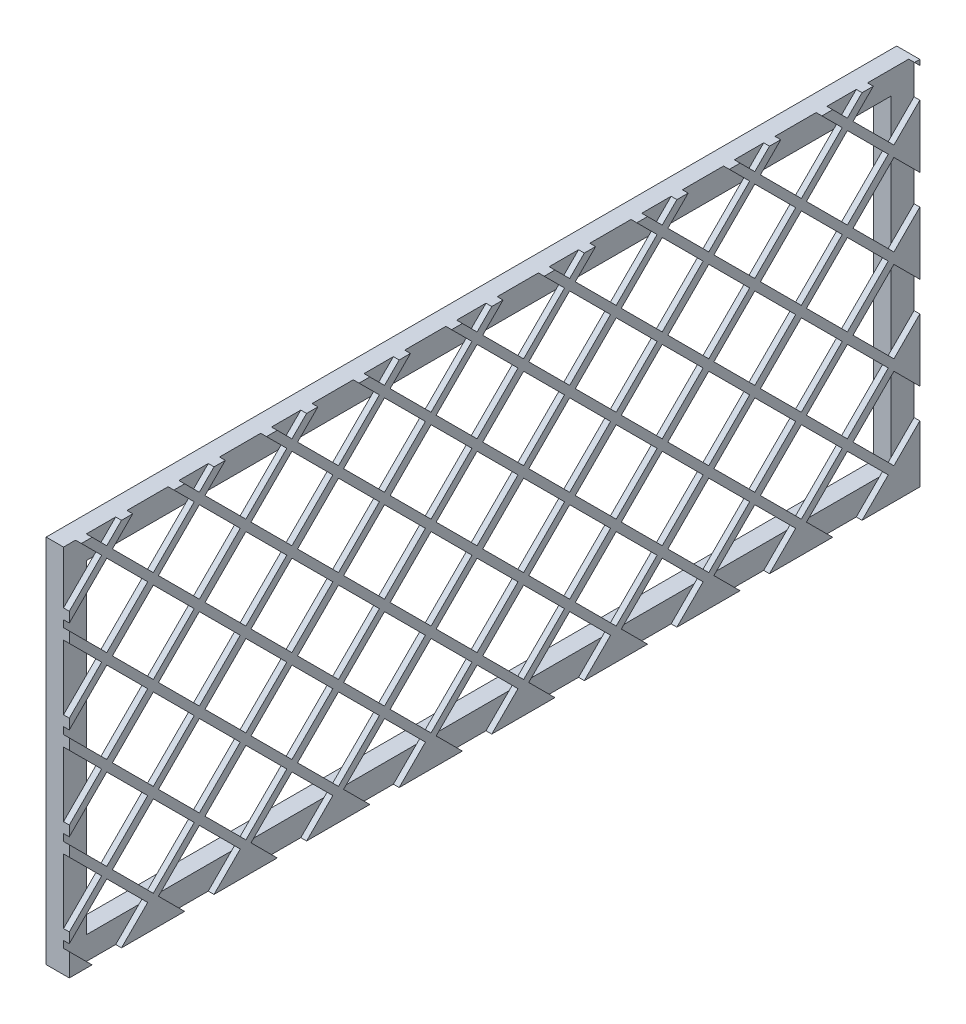
SolidWorks part; units mm, degrees
ref_plane "Front" through (0, 0, 0) normal (0, 0, 1) x (1, 0, 0)
ref_plane "Top" through (0, 0, 0) normal (0, 1, 0) x (1, 0, 0)
ref_plane "Right" through (0, 0, 0) normal (1, 0, 0) x (0, 0, -1)
sketch "Sketch1" plane through (0, 0, 0) normal (1, 0, 0) x (0, 0, -1)
  line L1 (-98.425, -3.313) -> (368.3, -3.313)
  line L2 (-98.425, -3.313) -> (-98.425, -206.513)
  line L3 (-98.425, -206.513) -> (368.3, -206.513)
  line L4 (368.3, -3.313) -> (368.3, -206.513)
  line L5 (-85.725, -16.013) -> (355.6, -16.013)
  line L6 (-85.725, -16.013) -> (-85.725, -193.813)
  line L7 (-85.725, -193.813) -> (355.6, -193.813)
  line L8 (355.6, -16.013) -> (355.6, -193.813)
  dimension "D1" = 12.7
  dimension "D2" = 12.7
  dimension "D3" = 12.7
  dimension "D4" = 12.7
  dimension "D5" = 203.2
  dimension "D6" = 466.725
extrude "Boss-Extrude1" add sketch "Sketch1" along normal blind 12.7
sketch "Sketch2" plane through (12.7, 0, 0) normal (1, 0, 0) x (0, 0, -1)
  line L1 (-85.725, -16.013) -> (355.6, -16.013)
  line L2 (-85.725, -16.013) -> (-85.725, -193.813)
  line L3 (-85.725, -193.813) -> (355.6, -193.813)
  line L4 (355.6, -16.013) -> (355.6, -193.813)
extrude "Boss-Extrude2" add sketch "Sketch2" against normal blind 3.175
sketch "Sketch3" plane through (9.525, 0, 0) normal (-1, 0, 0) x (0, 0, 1)
  line L0 (-350.9847, 163.4755) -> (-328.5341, 185.9261)
  line L1 (-328.5341, 185.9261) -> (-306.0835, 163.4755)
  line L2 (-350.9847, 163.4755) -> (-328.5341, 141.0249)
  line L3 (-328.5341, 141.0249) -> (-306.0835, 163.4755)
  line L8 (-354.0779, 211.1824) -> (-331.6272, 188.7318)
  line L9 (-331.6272, 188.7318) -> (-354.0779, 166.2811)
  line L10 (-354.0779, 166.2811) -> (-376.5285, 188.7318)
  line L11 (-376.5285, 188.7318) -> (-354.0779, 211.1824)
  line L12 (-300.1847, 163.4755) -> (-277.7341, 185.9261)
  line L13 (-277.7341, 185.9261) -> (-255.2835, 163.4755)
  line L14 (-300.1847, 163.4755) -> (-277.7341, 141.0249)
  line L15 (-277.7341, 141.0249) -> (-255.2835, 163.4755)
  line L16 (-280.8272, 188.7318) -> (-303.2779, 166.2811)
  line L17 (-303.2779, 166.2811) -> (-325.7285, 188.7318)
  line L18 (-325.7285, 188.7318) -> (-303.2779, 211.1824)
  line L19 (-303.2779, 211.1824) -> (-280.8272, 188.7318)
  line L20 (-249.3847, 163.4755) -> (-226.9341, 185.9261)
  line L21 (-226.9341, 185.9261) -> (-204.4835, 163.4755)
  line L22 (-249.3847, 163.4755) -> (-226.9341, 141.0249)
  line L23 (-226.9341, 141.0249) -> (-204.4835, 163.4755)
  line L24 (-230.0272, 188.7318) -> (-252.4779, 166.2811)
  line L25 (-252.4779, 166.2811) -> (-274.9285, 188.7318)
  line L26 (-274.9285, 188.7318) -> (-252.4779, 211.1824)
  line L27 (-252.4779, 211.1824) -> (-230.0272, 188.7318)
  line L28 (-198.5847, 163.4755) -> (-176.1341, 185.9261)
  line L29 (-176.1341, 185.9261) -> (-153.6835, 163.4755)
  line L30 (-198.5847, 163.4755) -> (-176.1341, 141.0249)
  line L31 (-176.1341, 141.0249) -> (-153.6835, 163.4755)
  line L32 (-179.2272, 188.7318) -> (-201.6779, 166.2811)
  line L33 (-201.6779, 166.2811) -> (-224.1285, 188.7318)
  line L34 (-224.1285, 188.7318) -> (-201.6779, 211.1824)
  line L35 (-201.6779, 211.1824) -> (-179.2272, 188.7318)
  line L36 (-147.7847, 163.4755) -> (-125.3341, 185.9261)
  line L37 (-125.3341, 185.9261) -> (-102.8835, 163.4755)
  line L38 (-147.7847, 163.4755) -> (-125.3341, 141.0249)
  line L39 (-125.3341, 141.0249) -> (-102.8835, 163.4755)
  line L40 (-128.4272, 188.7318) -> (-150.8779, 166.2811)
  line L41 (-150.8779, 166.2811) -> (-173.3285, 188.7318)
  line L42 (-173.3285, 188.7318) -> (-150.8779, 211.1824)
  line L43 (-150.8779, 211.1824) -> (-128.4272, 188.7318)
  line L44 (-96.9847, 163.4755) -> (-74.5341, 185.9261)
  line L45 (-74.5341, 185.9261) -> (-52.0835, 163.4755)
  line L46 (-96.9847, 163.4755) -> (-74.5341, 141.0249)
  line L47 (-74.5341, 141.0249) -> (-52.0835, 163.4755)
  line L48 (-77.6272, 188.7318) -> (-100.0779, 166.2811)
  line L49 (-100.0779, 166.2811) -> (-122.5285, 188.7318)
  line L50 (-122.5285, 188.7318) -> (-100.0779, 211.1824)
  line L51 (-100.0779, 211.1824) -> (-77.6272, 188.7318)
  line L52 (-46.1847, 163.4755) -> (-23.7341, 185.9261)
  line L53 (-23.7341, 185.9261) -> (-1.2835, 163.4755)
  line L54 (-46.1847, 163.4755) -> (-23.7341, 141.0249)
  line L55 (-23.7341, 141.0249) -> (-1.2835, 163.4755)
  line L56 (-26.8272, 188.7318) -> (-49.2779, 166.2811)
  line L57 (-49.2779, 166.2811) -> (-71.7285, 188.7318)
  line L58 (-71.7285, 188.7318) -> (-49.2779, 211.1824)
  line L59 (-49.2779, 211.1824) -> (-26.8272, 188.7318)
  line L60 (4.6153, 163.4755) -> (27.0659, 185.9261)
  line L61 (27.0659, 185.9261) -> (49.5165, 163.4755)
  line L62 (4.6153, 163.4755) -> (27.0659, 141.0249)
  line L63 (27.0659, 141.0249) -> (49.5165, 163.4755)
  line L64 (23.9728, 188.7318) -> (1.5221, 166.2811)
  line L65 (1.5221, 166.2811) -> (-20.9285, 188.7318)
  line L66 (-20.9285, 188.7318) -> (1.5221, 211.1824)
  line L67 (1.5221, 211.1824) -> (23.9728, 188.7318)
  line L68 (55.4153, 163.4755) -> (77.8659, 185.9261)
  line L69 (77.8659, 185.9261) -> (100.3165, 163.4755)
  line L70 (55.4153, 163.4755) -> (77.8659, 141.0249)
  line L71 (77.8659, 141.0249) -> (100.3165, 163.4755)
  line L72 (74.7728, 188.7318) -> (52.3221, 166.2811)
  line L73 (52.3221, 166.2811) -> (29.8715, 188.7318)
  line L74 (29.8715, 188.7318) -> (52.3221, 211.1824)
  line L75 (52.3221, 211.1824) -> (74.7728, 188.7318)
  line L76 (106.2153, 163.4755) -> (128.6659, 185.9261)
  line L77 (128.6659, 185.9261) -> (151.1165, 163.4755)
  line L78 (106.2153, 163.4755) -> (128.6659, 141.0249)
  line L79 (128.6659, 141.0249) -> (151.1165, 163.4755)
  line L80 (125.5728, 188.7318) -> (103.1221, 166.2811)
  line L81 (103.1221, 166.2811) -> (80.6715, 188.7318)
  line L82 (80.6715, 188.7318) -> (103.1221, 211.1824)
  line L83 (103.1221, 211.1824) -> (125.5728, 188.7318)
  line L84 (157.0153, 163.4755) -> (179.4659, 185.9261)
  line L85 (179.4659, 185.9261) -> (201.9165, 163.4755)
  line L86 (157.0153, 163.4755) -> (179.4659, 141.0249)
  line L87 (179.4659, 141.0249) -> (201.9165, 163.4755)
  line L88 (176.3728, 188.7318) -> (153.9221, 166.2811)
  line L89 (153.9221, 166.2811) -> (131.4715, 188.7318)
  line L90 (131.4715, 188.7318) -> (153.9221, 211.1824)
  line L91 (153.9221, 211.1824) -> (176.3728, 188.7318)
  line L92 (207.8153, 163.4755) -> (230.2659, 185.9261)
  line L93 (230.2659, 185.9261) -> (252.7165, 163.4755)
  line L94 (207.8153, 163.4755) -> (230.2659, 141.0249)
  line L95 (230.2659, 141.0249) -> (252.7165, 163.4755)
  line L96 (227.1728, 188.7318) -> (204.7221, 166.2811)
  line L97 (204.7221, 166.2811) -> (182.2715, 188.7318)
  line L98 (182.2715, 188.7318) -> (204.7221, 211.1824)
  line L99 (204.7221, 211.1824) -> (227.1728, 188.7318)
  line L100 (258.6153, 163.4755) -> (281.0659, 185.9261)
  line L101 (281.0659, 185.9261) -> (303.5165, 163.4755)
  line L102 (258.6153, 163.4755) -> (281.0659, 141.0249)
  line L103 (281.0659, 141.0249) -> (303.5165, 163.4755)
  line L104 (277.9728, 188.7318) -> (255.5221, 166.2811)
  line L105 (255.5221, 166.2811) -> (233.0715, 188.7318)
  line L106 (233.0715, 188.7318) -> (255.5221, 211.1824)
  line L107 (255.5221, 211.1824) -> (277.9728, 188.7318)
  line L108 (-300.1847, 112.6755) -> (-277.7341, 135.1261)
  line L109 (-277.7341, 135.1261) -> (-255.2835, 112.6755)
  line L110 (-300.1847, 112.6755) -> (-277.7341, 90.2249)
  line L111 (-277.7341, 90.2249) -> (-255.2835, 112.6755)
  line L112 (-280.8272, 137.9318) -> (-303.2779, 115.4811)
  line L113 (-303.2779, 115.4811) -> (-325.7285, 137.9318)
  line L114 (-325.7285, 137.9318) -> (-303.2779, 160.3824)
  line L115 (-303.2779, 160.3824) -> (-280.8272, 137.9318)
  line L116 (-249.3847, 112.6755) -> (-226.9341, 135.1261)
  line L117 (-226.9341, 135.1261) -> (-204.4835, 112.6755)
  line L118 (-249.3847, 112.6755) -> (-226.9341, 90.2249)
  line L119 (-226.9341, 90.2249) -> (-204.4835, 112.6755)
  line L120 (-230.0272, 137.9318) -> (-252.4779, 115.4811)
  line L121 (-252.4779, 115.4811) -> (-274.9285, 137.9318)
  line L122 (-274.9285, 137.9318) -> (-252.4779, 160.3824)
  line L123 (-252.4779, 160.3824) -> (-230.0272, 137.9318)
  line L124 (-198.5847, 112.6755) -> (-176.1341, 135.1261)
  line L125 (-176.1341, 135.1261) -> (-153.6835, 112.6755)
  line L126 (-198.5847, 112.6755) -> (-176.1341, 90.2249)
  line L127 (-176.1341, 90.2249) -> (-153.6835, 112.6755)
  line L128 (-179.2272, 137.9318) -> (-201.6779, 115.4811)
  line L129 (-201.6779, 115.4811) -> (-224.1285, 137.9318)
  line L130 (-224.1285, 137.9318) -> (-201.6779, 160.3824)
  line L131 (-201.6779, 160.3824) -> (-179.2272, 137.9318)
  line L132 (-147.7847, 112.6755) -> (-125.3341, 135.1261)
  line L133 (-125.3341, 135.1261) -> (-102.8835, 112.6755)
  line L134 (-147.7847, 112.6755) -> (-125.3341, 90.2249)
  line L135 (-125.3341, 90.2249) -> (-102.8835, 112.6755)
  line L136 (-128.4272, 137.9318) -> (-150.8779, 115.4811)
  line L137 (-150.8779, 115.4811) -> (-173.3285, 137.9318)
  line L138 (-173.3285, 137.9318) -> (-150.8779, 160.3824)
  line L139 (-150.8779, 160.3824) -> (-128.4272, 137.9318)
  line L140 (-96.9847, 112.6755) -> (-74.5341, 135.1261)
  line L141 (-74.5341, 135.1261) -> (-52.0835, 112.6755)
  line L142 (-96.9847, 112.6755) -> (-74.5341, 90.2249)
  line L143 (-74.5341, 90.2249) -> (-52.0835, 112.6755)
  line L144 (-77.6272, 137.9318) -> (-100.0779, 115.4811)
  line L145 (-100.0779, 115.4811) -> (-122.5285, 137.9318)
  line L146 (-122.5285, 137.9318) -> (-100.0779, 160.3824)
  line L147 (-100.0779, 160.3824) -> (-77.6272, 137.9318)
  line L148 (-46.1847, 112.6755) -> (-23.7341, 135.1261)
  line L149 (-23.7341, 135.1261) -> (-1.2835, 112.6755)
  line L150 (-46.1847, 112.6755) -> (-23.7341, 90.2249)
  line L151 (-23.7341, 90.2249) -> (-1.2835, 112.6755)
  line L152 (-26.8272, 137.9318) -> (-49.2779, 115.4811)
  line L153 (-49.2779, 115.4811) -> (-71.7285, 137.9318)
  line L154 (-71.7285, 137.9318) -> (-49.2779, 160.3824)
  line L155 (-49.2779, 160.3824) -> (-26.8272, 137.9318)
  line L156 (4.6153, 112.6755) -> (27.0659, 135.1261)
  line L157 (27.0659, 135.1261) -> (49.5165, 112.6755)
  line L158 (4.6153, 112.6755) -> (27.0659, 90.2249)
  line L159 (27.0659, 90.2249) -> (49.5165, 112.6755)
  line L160 (23.9728, 137.9318) -> (1.5221, 115.4811)
  line L161 (1.5221, 115.4811) -> (-20.9285, 137.9318)
  line L162 (-20.9285, 137.9318) -> (1.5221, 160.3824)
  line L163 (1.5221, 160.3824) -> (23.9728, 137.9318)
  line L164 (55.4153, 112.6755) -> (77.8659, 135.1261)
  line L165 (77.8659, 135.1261) -> (100.3165, 112.6755)
  line L166 (55.4153, 112.6755) -> (77.8659, 90.2249)
  line L167 (77.8659, 90.2249) -> (100.3165, 112.6755)
  line L168 (74.7728, 137.9318) -> (52.3221, 115.4811)
  line L169 (52.3221, 115.4811) -> (29.8715, 137.9318)
  line L170 (29.8715, 137.9318) -> (52.3221, 160.3824)
  line L171 (52.3221, 160.3824) -> (74.7728, 137.9318)
  line L172 (106.2153, 112.6755) -> (128.6659, 135.1261)
  line L173 (128.6659, 135.1261) -> (151.1165, 112.6755)
  line L174 (106.2153, 112.6755) -> (128.6659, 90.2249)
  line L175 (128.6659, 90.2249) -> (151.1165, 112.6755)
  line L176 (125.5728, 137.9318) -> (103.1221, 115.4811)
  line L177 (103.1221, 115.4811) -> (80.6715, 137.9318)
  line L178 (80.6715, 137.9318) -> (103.1221, 160.3824)
  line L179 (103.1221, 160.3824) -> (125.5728, 137.9318)
  line L180 (157.0153, 112.6755) -> (179.4659, 135.1261)
  line L181 (179.4659, 135.1261) -> (201.9165, 112.6755)
  line L182 (157.0153, 112.6755) -> (179.4659, 90.2249)
  line L183 (179.4659, 90.2249) -> (201.9165, 112.6755)
  line L184 (176.3728, 137.9318) -> (153.9221, 115.4811)
  line L185 (153.9221, 115.4811) -> (131.4715, 137.9318)
  line L186 (131.4715, 137.9318) -> (153.9221, 160.3824)
  line L187 (153.9221, 160.3824) -> (176.3728, 137.9318)
  line L188 (207.8153, 112.6755) -> (230.2659, 135.1261)
  line L189 (230.2659, 135.1261) -> (252.7165, 112.6755)
  line L190 (207.8153, 112.6755) -> (230.2659, 90.2249)
  line L191 (230.2659, 90.2249) -> (252.7165, 112.6755)
  line L192 (227.1728, 137.9318) -> (204.7221, 115.4811)
  line L193 (204.7221, 115.4811) -> (182.2715, 137.9318)
  line L194 (182.2715, 137.9318) -> (204.7221, 160.3824)
  line L195 (204.7221, 160.3824) -> (227.1728, 137.9318)
  line L196 (258.6153, 112.6755) -> (281.0659, 135.1261)
  line L197 (281.0659, 135.1261) -> (303.5165, 112.6755)
  line L198 (258.6153, 112.6755) -> (281.0659, 90.2249)
  line L199 (281.0659, 90.2249) -> (303.5165, 112.6755)
  line L200 (277.9728, 137.9318) -> (255.5221, 115.4811)
  line L201 (255.5221, 115.4811) -> (233.0715, 137.9318)
  line L202 (233.0715, 137.9318) -> (255.5221, 160.3824)
  line L203 (255.5221, 160.3824) -> (277.9728, 137.9318)
  line L204 (-300.1847, 61.8755) -> (-277.7341, 84.3261)
  line L205 (-277.7341, 84.3261) -> (-255.2835, 61.8755)
  line L206 (-300.1847, 61.8755) -> (-277.7341, 39.4249)
  line L207 (-277.7341, 39.4249) -> (-255.2835, 61.8755)
  line L208 (-280.8272, 87.1318) -> (-303.2779, 64.6811)
  line L209 (-303.2779, 64.6811) -> (-325.7285, 87.1318)
  line L210 (-325.7285, 87.1318) -> (-303.2779, 109.5824)
  line L211 (-303.2779, 109.5824) -> (-280.8272, 87.1318)
  line L212 (-249.3847, 61.8755) -> (-226.9341, 84.3261)
  line L213 (-226.9341, 84.3261) -> (-204.4835, 61.8755)
  line L214 (-249.3847, 61.8755) -> (-226.9341, 39.4249)
  line L215 (-226.9341, 39.4249) -> (-204.4835, 61.8755)
  line L216 (-230.0272, 87.1318) -> (-252.4779, 64.6811)
  line L217 (-252.4779, 64.6811) -> (-274.9285, 87.1318)
  line L218 (-274.9285, 87.1318) -> (-252.4779, 109.5824)
  line L219 (-252.4779, 109.5824) -> (-230.0272, 87.1318)
  line L220 (-198.5847, 61.8755) -> (-176.1341, 84.3261)
  line L221 (-176.1341, 84.3261) -> (-153.6835, 61.8755)
  line L222 (-198.5847, 61.8755) -> (-176.1341, 39.4249)
  line L223 (-176.1341, 39.4249) -> (-153.6835, 61.8755)
  line L224 (-179.2272, 87.1318) -> (-201.6779, 64.6811)
  line L225 (-201.6779, 64.6811) -> (-224.1285, 87.1318)
  line L226 (-224.1285, 87.1318) -> (-201.6779, 109.5824)
  line L227 (-201.6779, 109.5824) -> (-179.2272, 87.1318)
  line L228 (-147.7847, 61.8755) -> (-125.3341, 84.3261)
  line L229 (-125.3341, 84.3261) -> (-102.8835, 61.8755)
  line L230 (-147.7847, 61.8755) -> (-125.3341, 39.4249)
  line L231 (-125.3341, 39.4249) -> (-102.8835, 61.8755)
  line L232 (-128.4272, 87.1318) -> (-150.8779, 64.6811)
  line L233 (-150.8779, 64.6811) -> (-173.3285, 87.1318)
  line L234 (-173.3285, 87.1318) -> (-150.8779, 109.5824)
  line L235 (-150.8779, 109.5824) -> (-128.4272, 87.1318)
  line L236 (-96.9847, 61.8755) -> (-74.5341, 84.3261)
  line L237 (-74.5341, 84.3261) -> (-52.0835, 61.8755)
  line L238 (-96.9847, 61.8755) -> (-74.5341, 39.4249)
  line L239 (-74.5341, 39.4249) -> (-52.0835, 61.8755)
  line L240 (-77.6272, 87.1318) -> (-100.0779, 64.6811)
  line L241 (-100.0779, 64.6811) -> (-122.5285, 87.1318)
  line L242 (-122.5285, 87.1318) -> (-100.0779, 109.5824)
  line L243 (-100.0779, 109.5824) -> (-77.6272, 87.1318)
  line L244 (-46.1847, 61.8755) -> (-23.7341, 84.3261)
  line L245 (-23.7341, 84.3261) -> (-1.2835, 61.8755)
  line L246 (-46.1847, 61.8755) -> (-23.7341, 39.4249)
  line L247 (-23.7341, 39.4249) -> (-1.2835, 61.8755)
  line L248 (-26.8272, 87.1318) -> (-49.2779, 64.6811)
  line L249 (-49.2779, 64.6811) -> (-71.7285, 87.1318)
  line L250 (-71.7285, 87.1318) -> (-49.2779, 109.5824)
  line L251 (-49.2779, 109.5824) -> (-26.8272, 87.1318)
  line L252 (4.6153, 61.8755) -> (27.0659, 84.3261)
  line L253 (27.0659, 84.3261) -> (49.5165, 61.8755)
  line L254 (4.6153, 61.8755) -> (27.0659, 39.4249)
  line L255 (27.0659, 39.4249) -> (49.5165, 61.8755)
  line L256 (23.9728, 87.1318) -> (1.5221, 64.6811)
  line L257 (1.5221, 64.6811) -> (-20.9285, 87.1318)
  line L258 (-20.9285, 87.1318) -> (1.5221, 109.5824)
  line L259 (1.5221, 109.5824) -> (23.9728, 87.1318)
  line L260 (55.4153, 61.8755) -> (77.8659, 84.3261)
  line L261 (77.8659, 84.3261) -> (100.3165, 61.8755)
  line L262 (55.4153, 61.8755) -> (77.8659, 39.4249)
  line L263 (77.8659, 39.4249) -> (100.3165, 61.8755)
  line L264 (74.7728, 87.1318) -> (52.3221, 64.6811)
  line L265 (52.3221, 64.6811) -> (29.8715, 87.1318)
  line L266 (29.8715, 87.1318) -> (52.3221, 109.5824)
  line L267 (52.3221, 109.5824) -> (74.7728, 87.1318)
  line L268 (106.2153, 61.8755) -> (128.6659, 84.3261)
  line L269 (128.6659, 84.3261) -> (151.1165, 61.8755)
  line L270 (106.2153, 61.8755) -> (128.6659, 39.4249)
  line L271 (128.6659, 39.4249) -> (151.1165, 61.8755)
  line L272 (125.5728, 87.1318) -> (103.1221, 64.6811)
  line L273 (103.1221, 64.6811) -> (80.6715, 87.1318)
  line L274 (80.6715, 87.1318) -> (103.1221, 109.5824)
  line L275 (103.1221, 109.5824) -> (125.5728, 87.1318)
  line L276 (157.0153, 61.8755) -> (179.4659, 84.3261)
  line L277 (179.4659, 84.3261) -> (201.9165, 61.8755)
  line L278 (157.0153, 61.8755) -> (179.4659, 39.4249)
  line L279 (179.4659, 39.4249) -> (201.9165, 61.8755)
  line L280 (176.3728, 87.1318) -> (153.9221, 64.6811)
  line L281 (153.9221, 64.6811) -> (131.4715, 87.1318)
  line L282 (131.4715, 87.1318) -> (153.9221, 109.5824)
  line L283 (153.9221, 109.5824) -> (176.3728, 87.1318)
  line L284 (207.8153, 61.8755) -> (230.2659, 84.3261)
  line L285 (230.2659, 84.3261) -> (252.7165, 61.8755)
  line L286 (207.8153, 61.8755) -> (230.2659, 39.4249)
  line L287 (230.2659, 39.4249) -> (252.7165, 61.8755)
  line L288 (227.1728, 87.1318) -> (204.7221, 64.6811)
  line L289 (204.7221, 64.6811) -> (182.2715, 87.1318)
  line L290 (182.2715, 87.1318) -> (204.7221, 109.5824)
  line L291 (204.7221, 109.5824) -> (227.1728, 87.1318)
  line L292 (258.6153, 61.8755) -> (281.0659, 84.3261)
  line L293 (281.0659, 84.3261) -> (303.5165, 61.8755)
  line L294 (258.6153, 61.8755) -> (281.0659, 39.4249)
  line L295 (281.0659, 39.4249) -> (303.5165, 61.8755)
  line L296 (277.9728, 87.1318) -> (255.5221, 64.6811)
  line L297 (255.5221, 64.6811) -> (233.0715, 87.1318)
  line L298 (233.0715, 87.1318) -> (255.5221, 109.5824)
  line L299 (255.5221, 109.5824) -> (277.9728, 87.1318)
  line L300 (-300.1847, 11.0755) -> (-277.7341, 33.5261)
  line L301 (-277.7341, 33.5261) -> (-255.2835, 11.0755)
  line L302 (-300.1847, 11.0755) -> (-277.7341, -11.3751)
  line L303 (-277.7341, -11.3751) -> (-255.2835, 11.0755)
  line L304 (-280.8272, 36.3318) -> (-303.2779, 13.8811)
  line L305 (-303.2779, 13.8811) -> (-325.7285, 36.3318)
  line L306 (-325.7285, 36.3318) -> (-303.2779, 58.7824)
  line L307 (-303.2779, 58.7824) -> (-280.8272, 36.3318)
  line L308 (-249.3847, 11.0755) -> (-226.9341, 33.5261)
  line L309 (-226.9341, 33.5261) -> (-204.4835, 11.0755)
  line L310 (-249.3847, 11.0755) -> (-226.9341, -11.3751)
  line L311 (-226.9341, -11.3751) -> (-204.4835, 11.0755)
  line L312 (-230.0272, 36.3318) -> (-252.4779, 13.8811)
  line L313 (-252.4779, 13.8811) -> (-274.9285, 36.3318)
  line L314 (-274.9285, 36.3318) -> (-252.4779, 58.7824)
  line L315 (-252.4779, 58.7824) -> (-230.0272, 36.3318)
  line L316 (-198.5847, 11.0755) -> (-176.1341, 33.5261)
  line L317 (-176.1341, 33.5261) -> (-153.6835, 11.0755)
  line L318 (-198.5847, 11.0755) -> (-176.1341, -11.3751)
  line L319 (-176.1341, -11.3751) -> (-153.6835, 11.0755)
  line L320 (-179.2272, 36.3318) -> (-201.6779, 13.8811)
  line L321 (-201.6779, 13.8811) -> (-224.1285, 36.3318)
  line L322 (-224.1285, 36.3318) -> (-201.6779, 58.7824)
  line L323 (-201.6779, 58.7824) -> (-179.2272, 36.3318)
  line L324 (-147.7847, 11.0755) -> (-125.3341, 33.5261)
  line L325 (-125.3341, 33.5261) -> (-102.8835, 11.0755)
  line L326 (-147.7847, 11.0755) -> (-125.3341, -11.3751)
  line L327 (-125.3341, -11.3751) -> (-102.8835, 11.0755)
  line L328 (-128.4272, 36.3318) -> (-150.8779, 13.8811)
  line L329 (-150.8779, 13.8811) -> (-173.3285, 36.3318)
  line L330 (-173.3285, 36.3318) -> (-150.8779, 58.7824)
  line L331 (-150.8779, 58.7824) -> (-128.4272, 36.3318)
  line L332 (-96.9847, 11.0755) -> (-74.5341, 33.5261)
  line L333 (-74.5341, 33.5261) -> (-52.0835, 11.0755)
  line L334 (-96.9847, 11.0755) -> (-74.5341, -11.3751)
  line L335 (-74.5341, -11.3751) -> (-52.0835, 11.0755)
  line L336 (-77.6272, 36.3318) -> (-100.0779, 13.8811)
  line L337 (-100.0779, 13.8811) -> (-122.5285, 36.3318)
  line L338 (-122.5285, 36.3318) -> (-100.0779, 58.7824)
  line L339 (-100.0779, 58.7824) -> (-77.6272, 36.3318)
  line L340 (-46.1847, 11.0755) -> (-23.7341, 33.5261)
  line L341 (-23.7341, 33.5261) -> (-1.2835, 11.0755)
  line L342 (-46.1847, 11.0755) -> (-23.7341, -11.3751)
  line L343 (-23.7341, -11.3751) -> (-1.2835, 11.0755)
  line L344 (-26.8272, 36.3318) -> (-49.2779, 13.8811)
  line L345 (-49.2779, 13.8811) -> (-71.7285, 36.3318)
  line L346 (-71.7285, 36.3318) -> (-49.2779, 58.7824)
  line L347 (-49.2779, 58.7824) -> (-26.8272, 36.3318)
  line L348 (4.6153, 11.0755) -> (27.0659, 33.5261)
  line L349 (27.0659, 33.5261) -> (49.5165, 11.0755)
  line L350 (4.6153, 11.0755) -> (27.0659, -11.3751)
  line L351 (27.0659, -11.3751) -> (49.5165, 11.0755)
  line L352 (23.9728, 36.3318) -> (1.5221, 13.8811)
  line L353 (1.5221, 13.8811) -> (-20.9285, 36.3318)
  line L354 (-20.9285, 36.3318) -> (1.5221, 58.7824)
  line L355 (1.5221, 58.7824) -> (23.9728, 36.3318)
  line L356 (55.4153, 11.0755) -> (77.8659, 33.5261)
  line L357 (77.8659, 33.5261) -> (100.3165, 11.0755)
  line L358 (55.4153, 11.0755) -> (77.8659, -11.3751)
  line L359 (77.8659, -11.3751) -> (100.3165, 11.0755)
  line L360 (74.7728, 36.3318) -> (52.3221, 13.8811)
  line L361 (52.3221, 13.8811) -> (29.8715, 36.3318)
  line L362 (29.8715, 36.3318) -> (52.3221, 58.7824)
  line L363 (52.3221, 58.7824) -> (74.7728, 36.3318)
  line L364 (106.2153, 11.0755) -> (128.6659, 33.5261)
  line L365 (128.6659, 33.5261) -> (151.1165, 11.0755)
  line L366 (106.2153, 11.0755) -> (128.6659, -11.3751)
  line L367 (128.6659, -11.3751) -> (151.1165, 11.0755)
  line L368 (125.5728, 36.3318) -> (103.1221, 13.8811)
  line L369 (103.1221, 13.8811) -> (80.6715, 36.3318)
  line L370 (80.6715, 36.3318) -> (103.1221, 58.7824)
  line L371 (103.1221, 58.7824) -> (125.5728, 36.3318)
  line L372 (157.0153, 11.0755) -> (179.4659, 33.5261)
  line L373 (179.4659, 33.5261) -> (201.9165, 11.0755)
  line L374 (157.0153, 11.0755) -> (179.4659, -11.3751)
  line L375 (179.4659, -11.3751) -> (201.9165, 11.0755)
  line L376 (176.3728, 36.3318) -> (153.9221, 13.8811)
  line L377 (153.9221, 13.8811) -> (131.4715, 36.3318)
  line L378 (131.4715, 36.3318) -> (153.9221, 58.7824)
  line L379 (153.9221, 58.7824) -> (176.3728, 36.3318)
  line L380 (207.8153, 11.0755) -> (230.2659, 33.5261)
  line L381 (230.2659, 33.5261) -> (252.7165, 11.0755)
  line L382 (207.8153, 11.0755) -> (230.2659, -11.3751)
  line L383 (230.2659, -11.3751) -> (252.7165, 11.0755)
  line L384 (227.1728, 36.3318) -> (204.7221, 13.8811)
  line L385 (204.7221, 13.8811) -> (182.2715, 36.3318)
  line L386 (182.2715, 36.3318) -> (204.7221, 58.7824)
  line L387 (204.7221, 58.7824) -> (227.1728, 36.3318)
  line L388 (258.6153, 11.0755) -> (281.0659, 33.5261)
  line L389 (281.0659, 33.5261) -> (303.5165, 11.0755)
  line L390 (258.6153, 11.0755) -> (281.0659, -11.3751)
  line L391 (281.0659, -11.3751) -> (303.5165, 11.0755)
  line L392 (277.9728, 36.3318) -> (255.5221, 13.8811)
  line L393 (255.5221, 13.8811) -> (233.0715, 36.3318)
  line L394 (233.0715, 36.3318) -> (255.5221, 58.7824)
  line L395 (255.5221, 58.7824) -> (277.9728, 36.3318)
  line L396 (-300.1847, -39.7245) -> (-277.7341, -17.2739)
  line L397 (-277.7341, -17.2739) -> (-255.2835, -39.7245)
  line L398 (-300.1847, -39.7245) -> (-277.7341, -62.1751)
  line L399 (-277.7341, -62.1751) -> (-255.2835, -39.7245)
  line L400 (-280.8272, -14.4682) -> (-303.2779, -36.9189)
  line L401 (-303.2779, -36.9189) -> (-325.7285, -14.4682)
  line L402 (-325.7285, -14.4682) -> (-303.2779, 7.9824)
  line L403 (-303.2779, 7.9824) -> (-280.8272, -14.4682)
  line L404 (-249.3847, -39.7245) -> (-226.9341, -17.2739)
  line L405 (-226.9341, -17.2739) -> (-204.4835, -39.7245)
  line L406 (-249.3847, -39.7245) -> (-226.9341, -62.1751)
  line L407 (-226.9341, -62.1751) -> (-204.4835, -39.7245)
  line L408 (-230.0272, -14.4682) -> (-252.4779, -36.9189)
  line L409 (-252.4779, -36.9189) -> (-274.9285, -14.4682)
  line L410 (-274.9285, -14.4682) -> (-252.4779, 7.9824)
  line L411 (-252.4779, 7.9824) -> (-230.0272, -14.4682)
  line L412 (-198.5847, -39.7245) -> (-176.1341, -17.2739)
  line L413 (-176.1341, -17.2739) -> (-153.6835, -39.7245)
  line L414 (-198.5847, -39.7245) -> (-176.1341, -62.1751)
  line L415 (-176.1341, -62.1751) -> (-153.6835, -39.7245)
  line L416 (-179.2272, -14.4682) -> (-201.6779, -36.9189)
  line L417 (-201.6779, -36.9189) -> (-224.1285, -14.4682)
  line L418 (-224.1285, -14.4682) -> (-201.6779, 7.9824)
  line L419 (-201.6779, 7.9824) -> (-179.2272, -14.4682)
  line L420 (-147.7847, -39.7245) -> (-125.3341, -17.2739)
  line L421 (-125.3341, -17.2739) -> (-102.8835, -39.7245)
  line L422 (-147.7847, -39.7245) -> (-125.3341, -62.1751)
  line L423 (-125.3341, -62.1751) -> (-102.8835, -39.7245)
  line L424 (-128.4272, -14.4682) -> (-150.8779, -36.9189)
  line L425 (-150.8779, -36.9189) -> (-173.3285, -14.4682)
  line L426 (-173.3285, -14.4682) -> (-150.8779, 7.9824)
  line L427 (-150.8779, 7.9824) -> (-128.4272, -14.4682)
  line L428 (-96.9847, -39.7245) -> (-74.5341, -17.2739)
  line L429 (-74.5341, -17.2739) -> (-52.0835, -39.7245)
  line L430 (-96.9847, -39.7245) -> (-74.5341, -62.1751)
  line L431 (-74.5341, -62.1751) -> (-52.0835, -39.7245)
  line L432 (-77.6272, -14.4682) -> (-100.0779, -36.9189)
  line L433 (-100.0779, -36.9189) -> (-122.5285, -14.4682)
  line L434 (-122.5285, -14.4682) -> (-100.0779, 7.9824)
  line L435 (-100.0779, 7.9824) -> (-77.6272, -14.4682)
  line L436 (-46.1847, -39.7245) -> (-23.7341, -17.2739)
  line L437 (-23.7341, -17.2739) -> (-1.2835, -39.7245)
  line L438 (-46.1847, -39.7245) -> (-23.7341, -62.1751)
  line L439 (-23.7341, -62.1751) -> (-1.2835, -39.7245)
  line L440 (-26.8272, -14.4682) -> (-49.2779, -36.9189)
  line L441 (-49.2779, -36.9189) -> (-71.7285, -14.4682)
  line L442 (-71.7285, -14.4682) -> (-49.2779, 7.9824)
  line L443 (-49.2779, 7.9824) -> (-26.8272, -14.4682)
  line L444 (4.6153, -39.7245) -> (27.0659, -17.2739)
  line L445 (27.0659, -17.2739) -> (49.5165, -39.7245)
  line L446 (4.6153, -39.7245) -> (27.0659, -62.1751)
  line L447 (27.0659, -62.1751) -> (49.5165, -39.7245)
  line L448 (23.9728, -14.4682) -> (1.5221, -36.9189)
  line L449 (1.5221, -36.9189) -> (-20.9285, -14.4682)
  line L450 (-20.9285, -14.4682) -> (1.5221, 7.9824)
  line L451 (1.5221, 7.9824) -> (23.9728, -14.4682)
  line L452 (55.4153, -39.7245) -> (77.8659, -17.2739)
  line L453 (77.8659, -17.2739) -> (100.3165, -39.7245)
  line L454 (55.4153, -39.7245) -> (77.8659, -62.1751)
  line L455 (77.8659, -62.1751) -> (100.3165, -39.7245)
  line L456 (74.7728, -14.4682) -> (52.3221, -36.9189)
  line L457 (52.3221, -36.9189) -> (29.8715, -14.4682)
  line L458 (29.8715, -14.4682) -> (52.3221, 7.9824)
  line L459 (52.3221, 7.9824) -> (74.7728, -14.4682)
  line L460 (106.2153, -39.7245) -> (128.6659, -17.2739)
  line L461 (128.6659, -17.2739) -> (151.1165, -39.7245)
  line L462 (106.2153, -39.7245) -> (128.6659, -62.1751)
  line L463 (128.6659, -62.1751) -> (151.1165, -39.7245)
  line L464 (125.5728, -14.4682) -> (103.1221, -36.9189)
  line L465 (103.1221, -36.9189) -> (80.6715, -14.4682)
  line L466 (80.6715, -14.4682) -> (103.1221, 7.9824)
  line L467 (103.1221, 7.9824) -> (125.5728, -14.4682)
  line L468 (157.0153, -39.7245) -> (179.4659, -17.2739)
  line L469 (179.4659, -17.2739) -> (201.9165, -39.7245)
  line L470 (157.0153, -39.7245) -> (179.4659, -62.1751)
  line L471 (179.4659, -62.1751) -> (201.9165, -39.7245)
  line L472 (176.3728, -14.4682) -> (153.9221, -36.9189)
  line L473 (153.9221, -36.9189) -> (131.4715, -14.4682)
  line L474 (131.4715, -14.4682) -> (153.9221, 7.9824)
  line L475 (153.9221, 7.9824) -> (176.3728, -14.4682)
  line L476 (207.8153, -39.7245) -> (230.2659, -17.2739)
  line L477 (230.2659, -17.2739) -> (252.7165, -39.7245)
  line L478 (207.8153, -39.7245) -> (230.2659, -62.1751)
  line L479 (230.2659, -62.1751) -> (252.7165, -39.7245)
  line L480 (227.1728, -14.4682) -> (204.7221, -36.9189)
  line L481 (204.7221, -36.9189) -> (182.2715, -14.4682)
  line L482 (182.2715, -14.4682) -> (204.7221, 7.9824)
  line L483 (204.7221, 7.9824) -> (227.1728, -14.4682)
  line L484 (258.6153, -39.7245) -> (281.0659, -17.2739)
  line L485 (281.0659, -17.2739) -> (303.5165, -39.7245)
  line L486 (258.6153, -39.7245) -> (281.0659, -62.1751)
  line L487 (281.0659, -62.1751) -> (303.5165, -39.7245)
  line L488 (277.9728, -14.4682) -> (255.5221, -36.9189)
  line L489 (255.5221, -36.9189) -> (233.0715, -14.4682)
  line L490 (233.0715, -14.4682) -> (255.5221, 7.9824)
  line L491 (255.5221, 7.9824) -> (277.9728, -14.4682)
  line L492 (-300.1847, -90.5245) -> (-277.7341, -68.0739)
  line L493 (-277.7341, -68.0739) -> (-255.2835, -90.5245)
  line L494 (-300.1847, -90.5245) -> (-277.7341, -112.9751)
  line L495 (-277.7341, -112.9751) -> (-255.2835, -90.5245)
  line L496 (-280.8272, -65.2682) -> (-303.2779, -87.7189)
  line L497 (-303.2779, -87.7189) -> (-325.7285, -65.2682)
  line L498 (-325.7285, -65.2682) -> (-303.2779, -42.8176)
  line L499 (-303.2779, -42.8176) -> (-280.8272, -65.2682)
  line L500 (-249.3847, -90.5245) -> (-226.9341, -68.0739)
  line L501 (-226.9341, -68.0739) -> (-204.4835, -90.5245)
  line L502 (-249.3847, -90.5245) -> (-226.9341, -112.9751)
  line L503 (-226.9341, -112.9751) -> (-204.4835, -90.5245)
  line L504 (-230.0272, -65.2682) -> (-252.4779, -87.7189)
  line L505 (-252.4779, -87.7189) -> (-274.9285, -65.2682)
  line L506 (-274.9285, -65.2682) -> (-252.4779, -42.8176)
  line L507 (-252.4779, -42.8176) -> (-230.0272, -65.2682)
  line L508 (-198.5847, -90.5245) -> (-176.1341, -68.0739)
  line L509 (-176.1341, -68.0739) -> (-153.6835, -90.5245)
  line L510 (-198.5847, -90.5245) -> (-176.1341, -112.9751)
  line L511 (-176.1341, -112.9751) -> (-153.6835, -90.5245)
  line L512 (-179.2272, -65.2682) -> (-201.6779, -87.7189)
  line L513 (-201.6779, -87.7189) -> (-224.1285, -65.2682)
  line L514 (-224.1285, -65.2682) -> (-201.6779, -42.8176)
  line L515 (-201.6779, -42.8176) -> (-179.2272, -65.2682)
  line L516 (-147.7847, -90.5245) -> (-125.3341, -68.0739)
  line L517 (-125.3341, -68.0739) -> (-102.8835, -90.5245)
  line L518 (-147.7847, -90.5245) -> (-125.3341, -112.9751)
  line L519 (-125.3341, -112.9751) -> (-102.8835, -90.5245)
  line L520 (-128.4272, -65.2682) -> (-150.8779, -87.7189)
  line L521 (-150.8779, -87.7189) -> (-173.3285, -65.2682)
  line L522 (-173.3285, -65.2682) -> (-150.8779, -42.8176)
  line L523 (-150.8779, -42.8176) -> (-128.4272, -65.2682)
  line L524 (-96.9847, -90.5245) -> (-74.5341, -68.0739)
  line L525 (-74.5341, -68.0739) -> (-52.0835, -90.5245)
  line L526 (-96.9847, -90.5245) -> (-74.5341, -112.9751)
  line L527 (-74.5341, -112.9751) -> (-52.0835, -90.5245)
  line L528 (-77.6272, -65.2682) -> (-100.0779, -87.7189)
  line L529 (-100.0779, -87.7189) -> (-122.5285, -65.2682)
  line L530 (-122.5285, -65.2682) -> (-100.0779, -42.8176)
  line L531 (-100.0779, -42.8176) -> (-77.6272, -65.2682)
  line L532 (-46.1847, -90.5245) -> (-23.7341, -68.0739)
  line L533 (-23.7341, -68.0739) -> (-1.2835, -90.5245)
  line L534 (-46.1847, -90.5245) -> (-23.7341, -112.9751)
  line L535 (-23.7341, -112.9751) -> (-1.2835, -90.5245)
  line L536 (-26.8272, -65.2682) -> (-49.2779, -87.7189)
  line L537 (-49.2779, -87.7189) -> (-71.7285, -65.2682)
  line L538 (-71.7285, -65.2682) -> (-49.2779, -42.8176)
  line L539 (-49.2779, -42.8176) -> (-26.8272, -65.2682)
  line L540 (4.6153, -90.5245) -> (27.0659, -68.0739)
  line L541 (27.0659, -68.0739) -> (49.5165, -90.5245)
  line L542 (4.6153, -90.5245) -> (27.0659, -112.9751)
  line L543 (27.0659, -112.9751) -> (49.5165, -90.5245)
  line L544 (23.9728, -65.2682) -> (1.5221, -87.7189)
  line L545 (1.5221, -87.7189) -> (-20.9285, -65.2682)
  line L546 (-20.9285, -65.2682) -> (1.5221, -42.8176)
  line L547 (1.5221, -42.8176) -> (23.9728, -65.2682)
  line L548 (55.4153, -90.5245) -> (77.8659, -68.0739)
  line L549 (77.8659, -68.0739) -> (100.3165, -90.5245)
  line L550 (55.4153, -90.5245) -> (77.8659, -112.9751)
  line L551 (77.8659, -112.9751) -> (100.3165, -90.5245)
  line L552 (74.7728, -65.2682) -> (52.3221, -87.7189)
  line L553 (52.3221, -87.7189) -> (29.8715, -65.2682)
  line L554 (29.8715, -65.2682) -> (52.3221, -42.8176)
  line L555 (52.3221, -42.8176) -> (74.7728, -65.2682)
  line L556 (106.2153, -90.5245) -> (128.6659, -68.0739)
  line L557 (128.6659, -68.0739) -> (151.1165, -90.5245)
  line L558 (106.2153, -90.5245) -> (128.6659, -112.9751)
  line L559 (128.6659, -112.9751) -> (151.1165, -90.5245)
  line L560 (125.5728, -65.2682) -> (103.1221, -87.7189)
  line L561 (103.1221, -87.7189) -> (80.6715, -65.2682)
  line L562 (80.6715, -65.2682) -> (103.1221, -42.8176)
  line L563 (103.1221, -42.8176) -> (125.5728, -65.2682)
  line L564 (157.0153, -90.5245) -> (179.4659, -68.0739)
  line L565 (179.4659, -68.0739) -> (201.9165, -90.5245)
  line L566 (157.0153, -90.5245) -> (179.4659, -112.9751)
  line L567 (179.4659, -112.9751) -> (201.9165, -90.5245)
  line L568 (176.3728, -65.2682) -> (153.9221, -87.7189)
  line L569 (153.9221, -87.7189) -> (131.4715, -65.2682)
  line L570 (131.4715, -65.2682) -> (153.9221, -42.8176)
  line L571 (153.9221, -42.8176) -> (176.3728, -65.2682)
  line L572 (207.8153, -90.5245) -> (230.2659, -68.0739)
  line L573 (230.2659, -68.0739) -> (252.7165, -90.5245)
  line L574 (207.8153, -90.5245) -> (230.2659, -112.9751)
  line L575 (230.2659, -112.9751) -> (252.7165, -90.5245)
  line L576 (227.1728, -65.2682) -> (204.7221, -87.7189)
  line L577 (204.7221, -87.7189) -> (182.2715, -65.2682)
  line L578 (182.2715, -65.2682) -> (204.7221, -42.8176)
  line L579 (204.7221, -42.8176) -> (227.1728, -65.2682)
  line L580 (258.6153, -90.5245) -> (281.0659, -68.0739)
  line L581 (281.0659, -68.0739) -> (303.5165, -90.5245)
  line L582 (258.6153, -90.5245) -> (281.0659, -112.9751)
  line L583 (281.0659, -112.9751) -> (303.5165, -90.5245)
  line L584 (277.9728, -65.2682) -> (255.5221, -87.7189)
  line L585 (255.5221, -87.7189) -> (233.0715, -65.2682)
  line L586 (233.0715, -65.2682) -> (255.5221, -42.8176)
  line L587 (255.5221, -42.8176) -> (277.9728, -65.2682)
  line L588 (-300.1847, -141.3245) -> (-277.7341, -118.8739)
  line L589 (-277.7341, -118.8739) -> (-255.2835, -141.3245)
  line L590 (-300.1847, -141.3245) -> (-277.7341, -163.7751)
  line L591 (-277.7341, -163.7751) -> (-255.2835, -141.3245)
  line L592 (-280.8272, -116.0682) -> (-303.2779, -138.5189)
  line L593 (-303.2779, -138.5189) -> (-325.7285, -116.0682)
  line L594 (-325.7285, -116.0682) -> (-303.2779, -93.6176)
  line L595 (-303.2779, -93.6176) -> (-280.8272, -116.0682)
  line L596 (-249.3847, -141.3245) -> (-226.9341, -118.8739)
  line L597 (-226.9341, -118.8739) -> (-204.4835, -141.3245)
  line L598 (-249.3847, -141.3245) -> (-226.9341, -163.7751)
  line L599 (-226.9341, -163.7751) -> (-204.4835, -141.3245)
  line L600 (-230.0272, -116.0682) -> (-252.4779, -138.5189)
  line L601 (-252.4779, -138.5189) -> (-274.9285, -116.0682)
  line L602 (-274.9285, -116.0682) -> (-252.4779, -93.6176)
  line L603 (-252.4779, -93.6176) -> (-230.0272, -116.0682)
  line L604 (-198.5847, -141.3245) -> (-176.1341, -118.8739)
  line L605 (-176.1341, -118.8739) -> (-153.6835, -141.3245)
  line L606 (-198.5847, -141.3245) -> (-176.1341, -163.7751)
  line L607 (-176.1341, -163.7751) -> (-153.6835, -141.3245)
  line L608 (-179.2272, -116.0682) -> (-201.6779, -138.5189)
  line L609 (-201.6779, -138.5189) -> (-224.1285, -116.0682)
  line L610 (-224.1285, -116.0682) -> (-201.6779, -93.6176)
  line L611 (-201.6779, -93.6176) -> (-179.2272, -116.0682)
  line L612 (-147.7847, -141.3245) -> (-125.3341, -118.8739)
  line L613 (-125.3341, -118.8739) -> (-102.8835, -141.3245)
  line L614 (-147.7847, -141.3245) -> (-125.3341, -163.7751)
  line L615 (-125.3341, -163.7751) -> (-102.8835, -141.3245)
  line L616 (-128.4272, -116.0682) -> (-150.8779, -138.5189)
  line L617 (-150.8779, -138.5189) -> (-173.3285, -116.0682)
  line L618 (-173.3285, -116.0682) -> (-150.8779, -93.6176)
  line L619 (-150.8779, -93.6176) -> (-128.4272, -116.0682)
  line L620 (-96.9847, -141.3245) -> (-74.5341, -118.8739)
  line L621 (-74.5341, -118.8739) -> (-52.0835, -141.3245)
  line L622 (-96.9847, -141.3245) -> (-74.5341, -163.7751)
  line L623 (-74.5341, -163.7751) -> (-52.0835, -141.3245)
  line L624 (-77.6272, -116.0682) -> (-100.0779, -138.5189)
  line L625 (-100.0779, -138.5189) -> (-122.5285, -116.0682)
  line L626 (-122.5285, -116.0682) -> (-100.0779, -93.6176)
  line L627 (-100.0779, -93.6176) -> (-77.6272, -116.0682)
  line L628 (-46.1847, -141.3245) -> (-23.7341, -118.8739)
  line L629 (-23.7341, -118.8739) -> (-1.2835, -141.3245)
  line L630 (-46.1847, -141.3245) -> (-23.7341, -163.7751)
  line L631 (-23.7341, -163.7751) -> (-1.2835, -141.3245)
  line L632 (-26.8272, -116.0682) -> (-49.2779, -138.5189)
  line L633 (-49.2779, -138.5189) -> (-71.7285, -116.0682)
  line L634 (-71.7285, -116.0682) -> (-49.2779, -93.6176)
  line L635 (-49.2779, -93.6176) -> (-26.8272, -116.0682)
  line L636 (4.6153, -141.3245) -> (27.0659, -118.8739)
  line L637 (27.0659, -118.8739) -> (49.5165, -141.3245)
  line L638 (4.6153, -141.3245) -> (27.0659, -163.7751)
  line L639 (27.0659, -163.7751) -> (49.5165, -141.3245)
  line L640 (23.9728, -116.0682) -> (1.5221, -138.5189)
  line L641 (1.5221, -138.5189) -> (-20.9285, -116.0682)
  line L642 (-20.9285, -116.0682) -> (1.5221, -93.6176)
  line L643 (1.5221, -93.6176) -> (23.9728, -116.0682)
  line L644 (55.4153, -141.3245) -> (77.8659, -118.8739)
  line L645 (77.8659, -118.8739) -> (100.3165, -141.3245)
  line L646 (55.4153, -141.3245) -> (77.8659, -163.7751)
  line L647 (77.8659, -163.7751) -> (100.3165, -141.3245)
  line L648 (74.7728, -116.0682) -> (52.3221, -138.5189)
  line L649 (52.3221, -138.5189) -> (29.8715, -116.0682)
  line L650 (29.8715, -116.0682) -> (52.3221, -93.6176)
  line L651 (52.3221, -93.6176) -> (74.7728, -116.0682)
  line L652 (106.2153, -141.3245) -> (128.6659, -118.8739)
  line L653 (128.6659, -118.8739) -> (151.1165, -141.3245)
  line L654 (106.2153, -141.3245) -> (128.6659, -163.7751)
  line L655 (128.6659, -163.7751) -> (151.1165, -141.3245)
  line L656 (125.5728, -116.0682) -> (103.1221, -138.5189)
  line L657 (103.1221, -138.5189) -> (80.6715, -116.0682)
  line L658 (80.6715, -116.0682) -> (103.1221, -93.6176)
  line L659 (103.1221, -93.6176) -> (125.5728, -116.0682)
  line L660 (157.0153, -141.3245) -> (179.4659, -118.8739)
  line L661 (179.4659, -118.8739) -> (201.9165, -141.3245)
  line L662 (157.0153, -141.3245) -> (179.4659, -163.7751)
  line L663 (179.4659, -163.7751) -> (201.9165, -141.3245)
  line L664 (176.3728, -116.0682) -> (153.9221, -138.5189)
  line L665 (153.9221, -138.5189) -> (131.4715, -116.0682)
  line L666 (131.4715, -116.0682) -> (153.9221, -93.6176)
  line L667 (153.9221, -93.6176) -> (176.3728, -116.0682)
  line L668 (207.8153, -141.3245) -> (230.2659, -118.8739)
  line L669 (230.2659, -118.8739) -> (252.7165, -141.3245)
  line L670 (207.8153, -141.3245) -> (230.2659, -163.7751)
  line L671 (230.2659, -163.7751) -> (252.7165, -141.3245)
  line L672 (227.1728, -116.0682) -> (204.7221, -138.5189)
  line L673 (204.7221, -138.5189) -> (182.2715, -116.0682)
  line L674 (182.2715, -116.0682) -> (204.7221, -93.6176)
  line L675 (204.7221, -93.6176) -> (227.1728, -116.0682)
  line L676 (258.6153, -141.3245) -> (281.0659, -118.8739)
  line L677 (281.0659, -118.8739) -> (303.5165, -141.3245)
  line L678 (258.6153, -141.3245) -> (281.0659, -163.7751)
  line L679 (281.0659, -163.7751) -> (303.5165, -141.3245)
  line L680 (277.9728, -116.0682) -> (255.5221, -138.5189)
  line L681 (255.5221, -138.5189) -> (233.0715, -116.0682)
  line L682 (233.0715, -116.0682) -> (255.5221, -93.6176)
  line L683 (255.5221, -93.6176) -> (277.9728, -116.0682)
  line L684 (-300.1847, -192.1245) -> (-277.7341, -169.6739)
  line L685 (-277.7341, -169.6739) -> (-255.2835, -192.1245)
  line L686 (-300.1847, -192.1245) -> (-277.7341, -214.5751)
  line L687 (-277.7341, -214.5751) -> (-255.2835, -192.1245)
  line L688 (-280.8272, -166.8682) -> (-303.2779, -189.3189)
  line L689 (-303.2779, -189.3189) -> (-325.7285, -166.8682)
  line L690 (-325.7285, -166.8682) -> (-303.2779, -144.4176)
  line L691 (-303.2779, -144.4176) -> (-280.8272, -166.8682)
  line L692 (-249.3847, -192.1245) -> (-226.9341, -169.6739)
  line L693 (-226.9341, -169.6739) -> (-204.4835, -192.1245)
  line L694 (-249.3847, -192.1245) -> (-226.9341, -214.5751)
  line L695 (-226.9341, -214.5751) -> (-204.4835, -192.1245)
  line L696 (-230.0272, -166.8682) -> (-252.4779, -189.3189)
  line L697 (-252.4779, -189.3189) -> (-274.9285, -166.8682)
  line L698 (-274.9285, -166.8682) -> (-252.4779, -144.4176)
  line L699 (-252.4779, -144.4176) -> (-230.0272, -166.8682)
  line L700 (-198.5847, -192.1245) -> (-176.1341, -169.6739)
  line L701 (-176.1341, -169.6739) -> (-153.6835, -192.1245)
  line L702 (-198.5847, -192.1245) -> (-176.1341, -214.5751)
  line L703 (-176.1341, -214.5751) -> (-153.6835, -192.1245)
  line L704 (-179.2272, -166.8682) -> (-201.6779, -189.3189)
  line L705 (-201.6779, -189.3189) -> (-224.1285, -166.8682)
  line L706 (-224.1285, -166.8682) -> (-201.6779, -144.4176)
  line L707 (-201.6779, -144.4176) -> (-179.2272, -166.8682)
  line L708 (-147.7847, -192.1245) -> (-125.3341, -169.6739)
  line L709 (-125.3341, -169.6739) -> (-102.8835, -192.1245)
  line L710 (-147.7847, -192.1245) -> (-125.3341, -214.5751)
  line L711 (-125.3341, -214.5751) -> (-102.8835, -192.1245)
  line L712 (-128.4272, -166.8682) -> (-150.8779, -189.3189)
  line L713 (-150.8779, -189.3189) -> (-173.3285, -166.8682)
  line L714 (-173.3285, -166.8682) -> (-150.8779, -144.4176)
  line L715 (-150.8779, -144.4176) -> (-128.4272, -166.8682)
  line L716 (-96.9847, -192.1245) -> (-74.5341, -169.6739)
  line L717 (-74.5341, -169.6739) -> (-52.0835, -192.1245)
  line L718 (-96.9847, -192.1245) -> (-74.5341, -214.5751)
  line L719 (-74.5341, -214.5751) -> (-52.0835, -192.1245)
  line L720 (-77.6272, -166.8682) -> (-100.0779, -189.3189)
  line L721 (-100.0779, -189.3189) -> (-122.5285, -166.8682)
  line L722 (-122.5285, -166.8682) -> (-100.0779, -144.4176)
  line L723 (-100.0779, -144.4176) -> (-77.6272, -166.8682)
  line L724 (-46.1847, -192.1245) -> (-23.7341, -169.6739)
  line L725 (-23.7341, -169.6739) -> (-1.2835, -192.1245)
  line L726 (-46.1847, -192.1245) -> (-23.7341, -214.5751)
  line L727 (-23.7341, -214.5751) -> (-1.2835, -192.1245)
  line L728 (-26.8272, -166.8682) -> (-49.2779, -189.3189)
  line L729 (-49.2779, -189.3189) -> (-71.7285, -166.8682)
  line L730 (-71.7285, -166.8682) -> (-49.2779, -144.4176)
  line L731 (-49.2779, -144.4176) -> (-26.8272, -166.8682)
  line L732 (4.6153, -192.1245) -> (27.0659, -169.6739)
  line L733 (27.0659, -169.6739) -> (49.5165, -192.1245)
  line L734 (4.6153, -192.1245) -> (27.0659, -214.5751)
  line L735 (27.0659, -214.5751) -> (49.5165, -192.1245)
  line L736 (23.9728, -166.8682) -> (1.5221, -189.3189)
  line L737 (1.5221, -189.3189) -> (-20.9285, -166.8682)
  line L738 (-20.9285, -166.8682) -> (1.5221, -144.4176)
  line L739 (1.5221, -144.4176) -> (23.9728, -166.8682)
  line L740 (55.4153, -192.1245) -> (77.8659, -169.6739)
  line L741 (77.8659, -169.6739) -> (100.3165, -192.1245)
  line L742 (55.4153, -192.1245) -> (77.8659, -214.5751)
  line L743 (77.8659, -214.5751) -> (100.3165, -192.1245)
  line L744 (74.7728, -166.8682) -> (52.3221, -189.3189)
  line L745 (52.3221, -189.3189) -> (29.8715, -166.8682)
  line L746 (29.8715, -166.8682) -> (52.3221, -144.4176)
  line L747 (52.3221, -144.4176) -> (74.7728, -166.8682)
  line L748 (106.2153, -192.1245) -> (128.6659, -169.6739)
  line L749 (128.6659, -169.6739) -> (151.1165, -192.1245)
  line L750 (106.2153, -192.1245) -> (128.6659, -214.5751)
  line L751 (128.6659, -214.5751) -> (151.1165, -192.1245)
  line L752 (125.5728, -166.8682) -> (103.1221, -189.3189)
  line L753 (103.1221, -189.3189) -> (80.6715, -166.8682)
  line L754 (80.6715, -166.8682) -> (103.1221, -144.4176)
  line L755 (103.1221, -144.4176) -> (125.5728, -166.8682)
  line L756 (157.0153, -192.1245) -> (179.4659, -169.6739)
  line L757 (179.4659, -169.6739) -> (201.9165, -192.1245)
  line L758 (157.0153, -192.1245) -> (179.4659, -214.5751)
  line L759 (179.4659, -214.5751) -> (201.9165, -192.1245)
  line L760 (176.3728, -166.8682) -> (153.9221, -189.3189)
  line L761 (153.9221, -189.3189) -> (131.4715, -166.8682)
  line L762 (131.4715, -166.8682) -> (153.9221, -144.4176)
  line L763 (153.9221, -144.4176) -> (176.3728, -166.8682)
  line L764 (207.8153, -192.1245) -> (230.2659, -169.6739)
  line L765 (230.2659, -169.6739) -> (252.7165, -192.1245)
  line L766 (207.8153, -192.1245) -> (230.2659, -214.5751)
  line L767 (230.2659, -214.5751) -> (252.7165, -192.1245)
  line L768 (227.1728, -166.8682) -> (204.7221, -189.3189)
  line L769 (204.7221, -189.3189) -> (182.2715, -166.8682)
  line L770 (182.2715, -166.8682) -> (204.7221, -144.4176)
  line L771 (204.7221, -144.4176) -> (227.1728, -166.8682)
  line L772 (258.6153, -192.1245) -> (281.0659, -169.6739)
  line L773 (281.0659, -169.6739) -> (303.5165, -192.1245)
  line L774 (258.6153, -192.1245) -> (281.0659, -214.5751)
  line L775 (281.0659, -214.5751) -> (303.5165, -192.1245)
  line L776 (277.9728, -166.8682) -> (255.5221, -189.3189)
  line L777 (255.5221, -189.3189) -> (233.0715, -166.8682)
  line L778 (233.0715, -166.8682) -> (255.5221, -144.4176)
  line L779 (255.5221, -144.4176) -> (277.9728, -166.8682)
  line L780 (-350.9847, 112.6755) -> (-328.5341, 135.1261)
  line L781 (-328.5341, 135.1261) -> (-306.0835, 112.6755)
  line L782 (-350.9847, 112.6755) -> (-328.5341, 90.2249)
  line L783 (-328.5341, 90.2249) -> (-306.0835, 112.6755)
  line L784 (-331.6272, 137.9318) -> (-354.0779, 115.4811)
  line L785 (-354.0779, 115.4811) -> (-376.5285, 137.9318)
  line L786 (-376.5285, 137.9318) -> (-354.0779, 160.3824)
  line L787 (-354.0779, 160.3824) -> (-331.6272, 137.9318)
  line L788 (-350.9847, 61.8755) -> (-328.5341, 84.3261)
  line L789 (-328.5341, 84.3261) -> (-306.0835, 61.8755)
  line L790 (-350.9847, 61.8755) -> (-328.5341, 39.4249)
  line L791 (-328.5341, 39.4249) -> (-306.0835, 61.8755)
  line L792 (-331.6272, 87.1318) -> (-354.0779, 64.6811)
  line L793 (-354.0779, 64.6811) -> (-376.5285, 87.1318)
  line L794 (-376.5285, 87.1318) -> (-354.0779, 109.5824)
  line L795 (-354.0779, 109.5824) -> (-331.6272, 87.1318)
  line L796 (-350.9847, 11.0755) -> (-328.5341, 33.5261)
  line L797 (-328.5341, 33.5261) -> (-306.0835, 11.0755)
  line L798 (-350.9847, 11.0755) -> (-328.5341, -11.3751)
  line L799 (-328.5341, -11.3751) -> (-306.0835, 11.0755)
  line L800 (-331.6272, 36.3318) -> (-354.0779, 13.8811)
  line L801 (-354.0779, 13.8811) -> (-376.5285, 36.3318)
  line L802 (-376.5285, 36.3318) -> (-354.0779, 58.7824)
  line L803 (-354.0779, 58.7824) -> (-331.6272, 36.3318)
  line L804 (-350.9847, -39.7245) -> (-328.5341, -17.2739)
  line L805 (-328.5341, -17.2739) -> (-306.0835, -39.7245)
  line L806 (-350.9847, -39.7245) -> (-328.5341, -62.1751)
  line L807 (-328.5341, -62.1751) -> (-306.0835, -39.7245)
  line L808 (-331.6272, -14.4682) -> (-354.0779, -36.9189)
  line L809 (-354.0779, -36.9189) -> (-376.5285, -14.4682)
  line L810 (-376.5285, -14.4682) -> (-354.0779, 7.9824)
  line L811 (-354.0779, 7.9824) -> (-331.6272, -14.4682)
  line L812 (-350.9847, -90.5245) -> (-328.5341, -68.0739)
  line L813 (-328.5341, -68.0739) -> (-306.0835, -90.5245)
  line L814 (-350.9847, -90.5245) -> (-328.5341, -112.9751)
  line L815 (-328.5341, -112.9751) -> (-306.0835, -90.5245)
  line L816 (-331.6272, -65.2682) -> (-354.0779, -87.7189)
  line L817 (-354.0779, -87.7189) -> (-376.5285, -65.2682)
  line L818 (-376.5285, -65.2682) -> (-354.0779, -42.8176)
  line L819 (-354.0779, -42.8176) -> (-331.6272, -65.2682)
  line L820 (-350.9847, -141.3245) -> (-328.5341, -118.8739)
  line L821 (-328.5341, -118.8739) -> (-306.0835, -141.3245)
  line L822 (-350.9847, -141.3245) -> (-328.5341, -163.7751)
  line L823 (-328.5341, -163.7751) -> (-306.0835, -141.3245)
  line L824 (-331.6272, -116.0682) -> (-354.0779, -138.5189)
  line L825 (-354.0779, -138.5189) -> (-376.5285, -116.0682)
  line L826 (-376.5285, -116.0682) -> (-354.0779, -93.6176)
  line L827 (-354.0779, -93.6176) -> (-331.6272, -116.0682)
  line L828 (-350.9847, -192.1245) -> (-328.5341, -169.6739)
  line L829 (-328.5341, -169.6739) -> (-306.0835, -192.1245)
  line L830 (-350.9847, -192.1245) -> (-328.5341, -214.5751)
  line L831 (-328.5341, -214.5751) -> (-306.0835, -192.1245)
  line L832 (-331.6272, -166.8682) -> (-354.0779, -189.3189)
  line L833 (-354.0779, -189.3189) -> (-376.5285, -166.8682)
  line L834 (-376.5285, -166.8682) -> (-354.0779, -144.4176)
  line L835 (-354.0779, -144.4176) -> (-331.6272, -166.8682)
  dimension "D1" = 13
  dimension "D2" = 8
extrude "Cut-Extrude1" cut sketch "Sketch3" against normal blind 3.175
